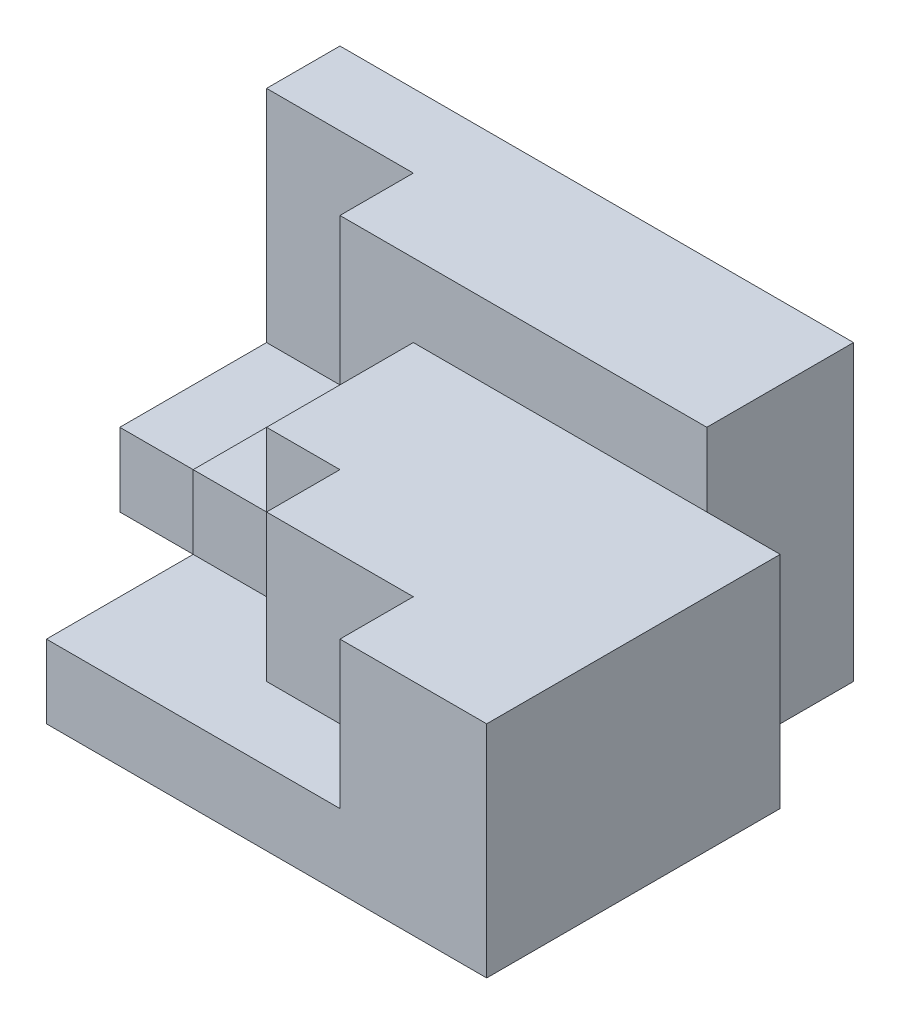
SolidWorks part; units mm, degrees
ref_plane "Front Plane" through (0, 0, 0) normal (0, 0, 1) x (1, 0, 0)
ref_plane "Top Plane" through (0, 0, 0) normal (0, 1, 0) x (1, 0, 0)
ref_plane "Right Plane" through (0, 0, 0) normal (1, 0, 0) x (0, 0, -1)
sketch "Sketch1" plane through (0, 0, 0) normal (0, 1, 0) x (1, 0, 0)
  line L0 (0, 0) -> (-10, 0)
  line L1 (-10, 0) -> (-10, 20)
  line L2 (-10, 20) -> (-80, 20)
  line L3 (-80, 20) -> (-80, -10)
  line L4 (-80, -10) -> (-60, -10)
  line L5 (-60, -10) -> (-60, -40)
  line L6 (-60, -40) -> (0, -40)
  line L7 (0, -40) -> (0, 0)
  dimension "D1" = 40
  dimension "D2" = 10
  dimension "D3" = 20
  dimension "D4" = 70
  dimension "D5" = 30
  dimension "D6" = 20
extrude "Boss-Extrude1" add sketch "Sketch1" along normal blind 10
sketch "Sketch2" plane through (0, 10, 0) normal (0, 1, 0) x (1, 0, 0)
  line L0 (-10, 20) -> (-10, 0)
  line L1 (-10, 0) -> (0, 0)
  line L2 (0, 0) -> (0, -40)
  line L3 (0, -40) -> (-20, -40)
  line L4 (-60, -40) -> (0, -40) construction
  line L5 (-20, -40) -> (-20, -30)
  line L6 (-20, -30) -> (-40, -30)
  line L7 (-40, -30) -> (-40, -20)
  line L8 (-40, -20) -> (-60, -20)
  line L9 (-60, -10) -> (-60, -40) construction
  line L10 (-60, 20) -> (-80, 20)
  line L11 (-10, 20) -> (-80, 20) construction
  line L12 (-60, 20) -> (-10, 20)
  line L13 (-80, 20) -> (-80, 10)
  line L14 (-80, 20) -> (-80, -10) construction
  line L15 (-80, 10) -> (-60, 10)
  line L16 (-60, 10) -> (-60, -10)
  line L17 (-60, -10) -> (-60, -20)
  dimension "D1" = 20
  dimension "D2" = 10
  dimension "D3" = 20
  dimension "D4" = 10
  dimension "D5" = 10
extrude "Boss-Extrude2" add sketch "Sketch2" along normal blind 20
sketch "Sketch3" plane through (0, 30, 0) normal (0, 1, 0) x (1, 0, 0)
  line L0 (-80, 20) -> (-10, 20)
  line L1 (-10, 20) -> (-10, 0)
  line L2 (-10, 0) -> (-10, 20) construction
  line L3 (-10, 0) -> (-60, 0)
  line L4 (-60, 10) -> (-60, -10) construction
  line L5 (-60, 0) -> (-60, 10)
  line L6 (-60, 10) -> (-80, 10)
  line L7 (-80, 10) -> (-80, 20)
  dimension "D1" = 10
extrude "Boss-Extrude3" add sketch "Sketch3" along normal blind 10
sketch "Sketch4" plane through (0, 30, 0) normal (0, 1, 0) x (1, 0, 0)
  line L1 (-50, -26.2912) -> (-60, -26.2912)
  line L2 (-50, -26.2912) -> (-50, 0)
  line L3 (-50, 0) -> (-60, 0)
  line L4 (-60, -26.2912) -> (-60, 0)
  dimension "D1" = 10
extrude "Cut-Extrude1" cut sketch "Sketch4" against normal blind 10
